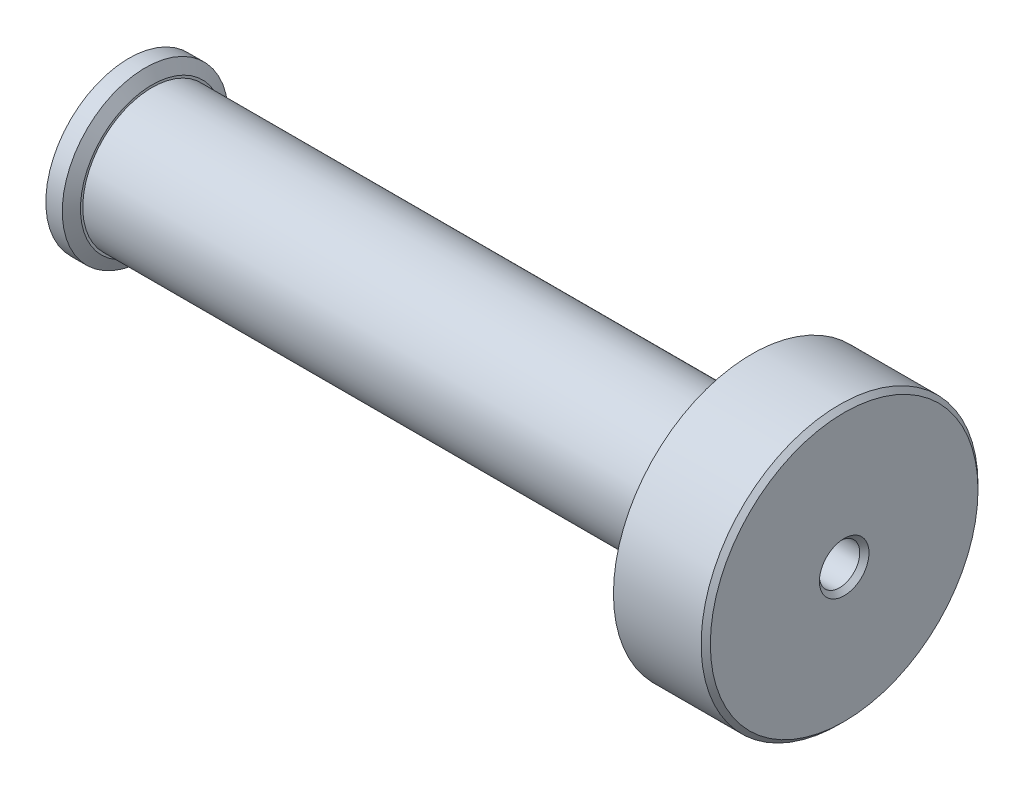
SolidWorks part; units mm, degrees
material "Custom Plastic"
ref_plane "Front Plane" through (0, 0, 0) normal (0, 0, 1) x (1, 0, 0)
ref_plane "Top Plane" through (0, 0, 0) normal (0, 1, 0) x (1, 0, 0)
ref_plane "Right Plane" through (0, 0, 0) normal (1, 0, 0) x (0, 0, -1)
sketch "Sketch3" plane through (0, 0, 0) normal (0, 1, 0) x (1, 0, 0)
  line L0 (0, 0) -> (-62, 0) construction
  line L1 (-62, 0) -> (-62, 7.2)
  line L2 (-62, 7.2) -> (-60, 7.2)
  line L3 (-60, 7.2) -> (-60, 6)
  line L4 (-60, 6) -> (-10, 6)
  line L5 (-10, 6) -> (-10, 12)
  line L6 (-10, 12) -> (0, 12)
  line L7 (0, 12) -> (0, 0)
  line L8 (0, 0) -> (-62, 0)
  dimension "D1" = 24
  dimension "D2" = 12
  dimension "D3" = 10
  dimension "D4" = 50
  dimension "D5" = 2
  dimension "D6" = 1.2
revolve "Revolve1" add sketch "Sketch3" angle 360 about L0
chamfer "Chamfer1" distance 1 angle 30 1 edges at (-60, 0, -7.2)
chamfer "Chamfer2" distance 2 angle 60 1 edges at (-10, 0, -12)
sketch "Sketch4" plane through (-62, 0, 0) normal (-1, 0, 0) x (0, 0, 1)
  circle A0 centre (0, 0) radius 4.8
  circle A1 centre (0, 0) radius 6 construction
  dimension "D1" = 1.2
extrude "Cut-Extrude1" cut sketch "Sketch4" against normal offset from surface (53 mm away) 9 up to face at (0, 0, -12)
sketch "Sketch5" plane through (-9, 0, 0) normal (-1, 0, 0) x (0, 0, 1)
  circle A0 centre (0, 0) radius 1.75
  dimension "D1" = 3.5
extrude "Cut-Extrude2" cut sketch "Sketch5" against normal through all
chamfer "Chamfer3" distance 0.4 angle 45 2 edges at (0, 0, -12) (0, 0, 1.75)
